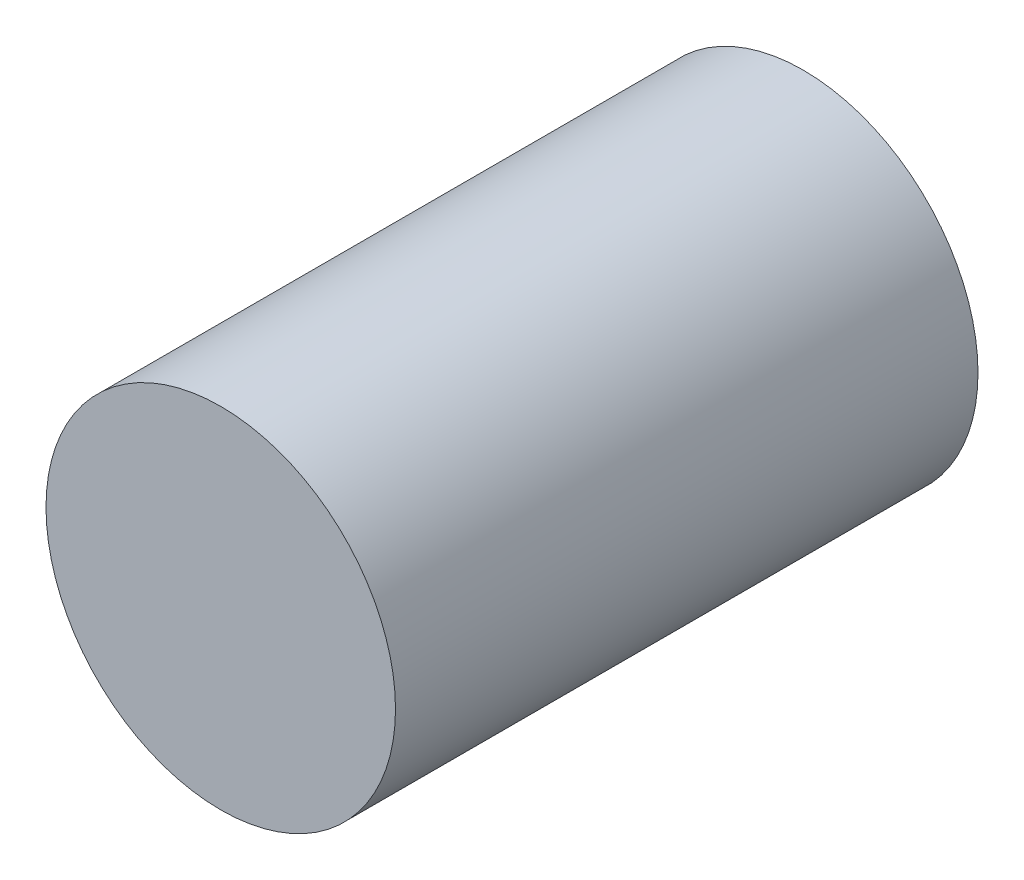
SolidWorks part; units mm, degrees
ref_plane "Front Plane" through (0, 0, 0) normal (0, 0, 1) x (1, 0, 0)
ref_plane "Top Plane" through (0, 0, 0) normal (0, 1, 0) x (1, 0, 0)
ref_plane "Right Plane" through (0, 0, 0) normal (1, 0, 0) x (0, 0, -1)
sketch "Sketch1" plane through (0, 0, 0) normal (0, 0, 1) x (1, 0, 0)
  circle A0 centre (0, 0) radius 15
  dimension "D1" = 30
extrude "Boss-Extrude2" add sketch "Sketch1" along normal blind 50
sketch "Sketch3" plane through (0, 0, 0) normal (0, 1, 0) x (1, 0, 0)
  line L0 (-16.3323, -24.9254) -> (19.2408, -24.9254) construction
  line L1 (0, 0) -> (0, -51.1764) construction
  circle A0 centre (0, -24.9254) radius 5
extrude "Cut-Extrude2" cut sketch "Sketch3" against normal blind 50
